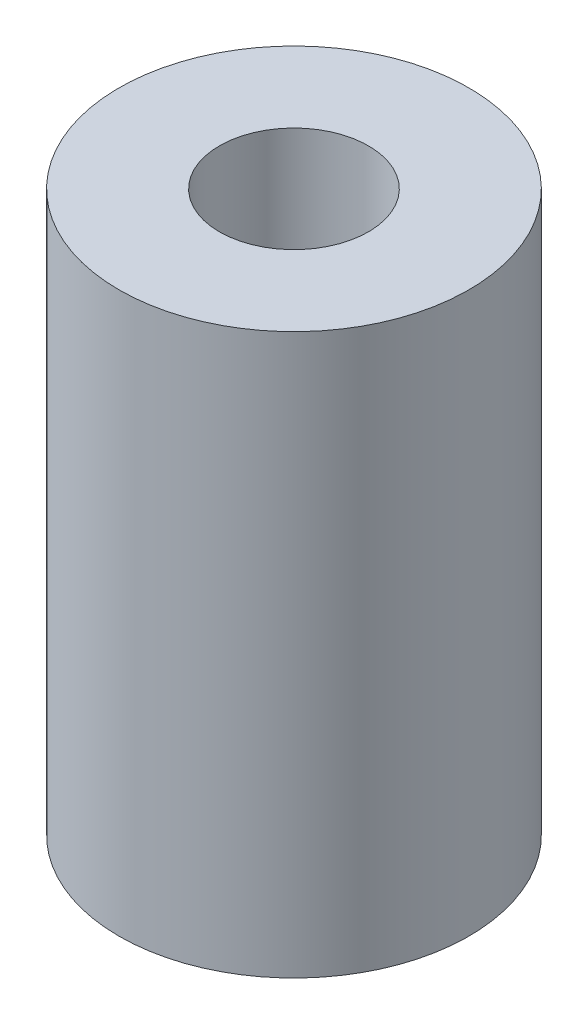
SolidWorks part; units mm, degrees
ref_plane "Front Plane" through (0, 0, 0) normal (0, 0, 1) x (1, 0, 0)
ref_plane "Top Plane" through (0, 0, 0) normal (0, 1, 0) x (1, 0, 0)
ref_plane "Right Plane" through (0, 0, 0) normal (1, 0, 0) x (0, 0, -1)
sketch "Sketch1" plane through (0, 0, 0) normal (0, 1, 0) x (1, 0, 0)
  circle A0 centre (0, 0) radius 3.175
  dimension "D1" = 6.35
extrude "Boss-Extrude1" add sketch "Sketch1" along normal blind 10.16
hole_wizard "#2 Clearance Hole1" positions "Sketch2" profile "Sketch3" hole size "#2" standard "ANSI Inch" end condition through all
sketch "Sketch2" plane through (0, 10.16, 0) normal (0, 1, 0) x (1, 0, 0)
  point P0 (0, 0)
sketch "Sketch3" plane through (0, 10.16, 0) normal (1, 0, 0) x (0, 0, 1)
  line L0 (0, 0) -> (0, 10.16)
  line L1 (0, 10.16) -> (1.3525, 10.16)
  line L2 (1.3525, 10.16) -> (1.3525, 0)
  line L5 (1.3525, 0) -> (0, 0)
  line L11 (0, -6.35) -> (0, 107.95) construction
  dimension "Thru Hole Dia." = 2.7051
  dimension "Thru Hole Depth" = 10.16
